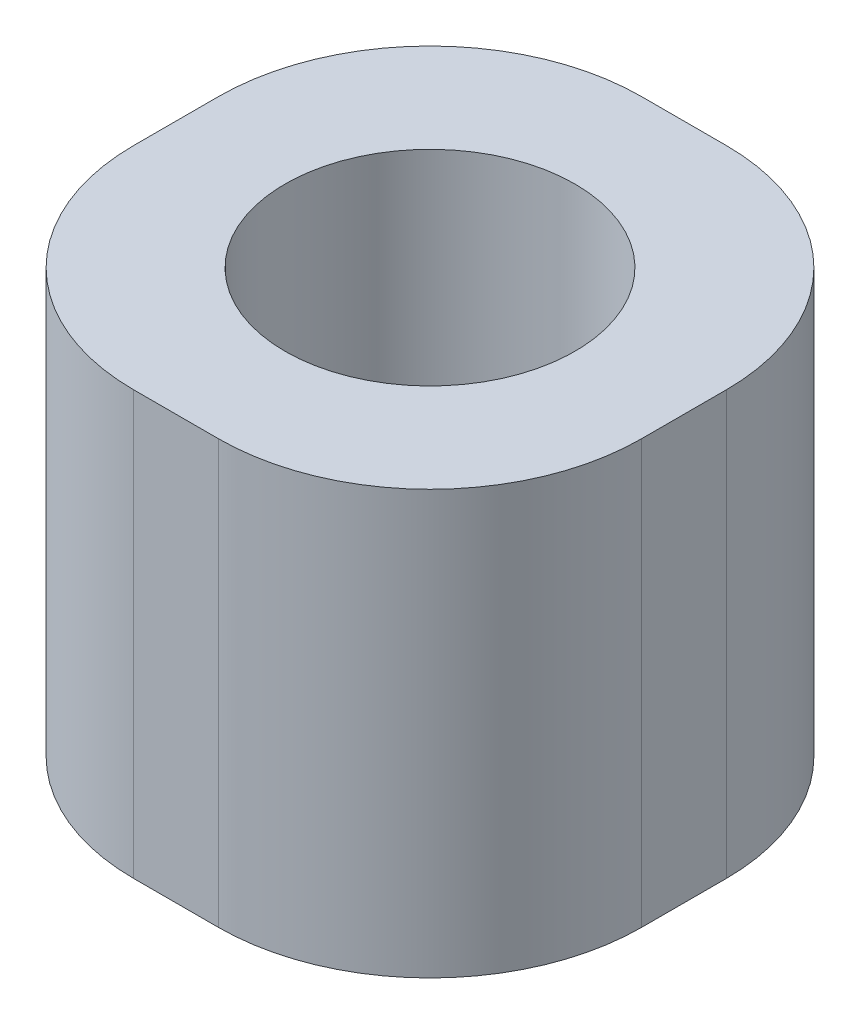
SolidWorks part; units mm, degrees
ref_plane "Front Plane" through (0, 0, 0) normal (0, 0, 1) x (1, 0, 0)
ref_plane "Top Plane" through (0, 0, 0) normal (0, 1, 0) x (1, 0, 0)
ref_plane "Right Plane" through (0, 0, 0) normal (1, 0, 0) x (0, 0, -1)
sketch "Sketch1" plane through (0, 0, 0) normal (0, 1, 0) x (1, 0, 0)
  line L1 (6, -6) -> (-6, -6)
  line L2 (6, -6) -> (6, 6)
  line L3 (6, 6) -> (-6, 6)
  line L4 (-6, -6) -> (-6, 6)
  line L5 (6, -6) -> (-6, 6) construction
  line L6 (6, 6) -> (-6, -6) construction
  point P0 (0, 0)
  dimension "D1" = 12
  dimension "D2" = 12
extrude "Boss-Extrude1" add sketch "Sketch1" along normal blind 10
fillet "Fillet1" radius 5 4 edges at (-6, 5, -6) (6, 5, -6) (-6, 5, 6) (6, 5, 6)
sketch "Sketch2" plane through (0, 10, 0) normal (0, 1, 0) x (1, 0, 0)
  circle A0 centre (0, 0) radius 2
  dimension "D1" = 4
extrude "Cut-Extrude1" cut sketch "Sketch2" against normal through all
sketch "Sketch3" plane through (0, 10, 0) normal (0, 1, 0) x (1, 0, 0)
  circle A0 centre (0, 0) radius 3.425
  dimension "D1" = 6.85
extrude "Cut-Extrude2" cut sketch "Sketch3" against normal blind 6.35
